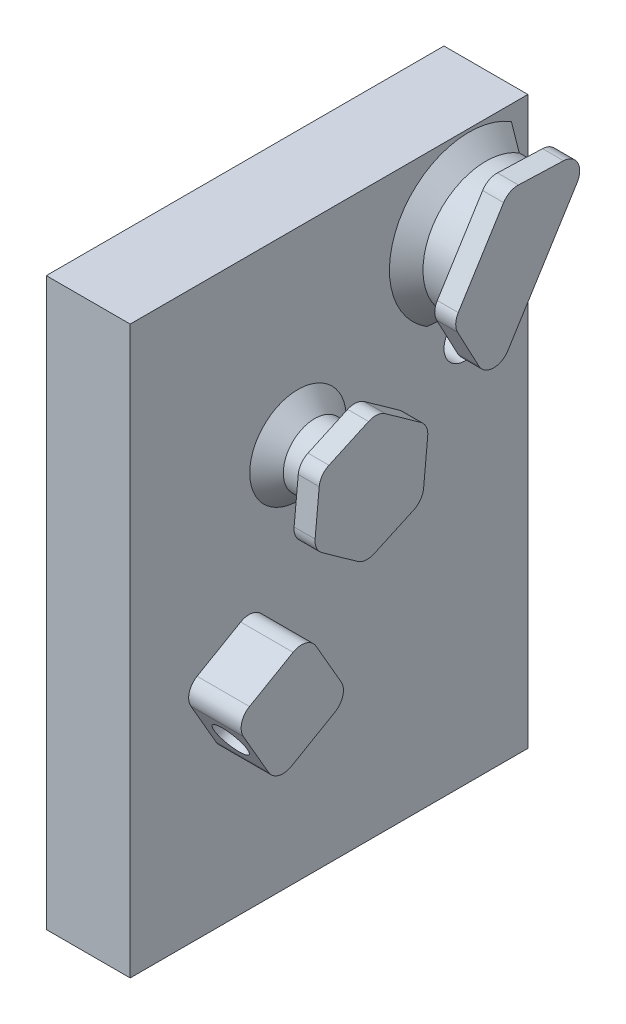
SolidWorks part; units mm, degrees
ref_plane "Front Plane" through (0, 0, 0) normal (0, 0, 1) x (1, 0, 0)
ref_plane "Top Plane" through (0, 0, 0) normal (0, 1, 0) x (1, 0, 0)
ref_plane "Right Plane" through (0, 0, 0) normal (1, 0, 0) x (0, 0, -1)
sketch "Sketch1" plane through (0, 0, 0) normal (1, 0, 0) x (0, 0, -1)
  line L0 (25.527, 46.2915) -> (60.198, 46.2915) construction
  line L1 (0, 0) -> (60.198, 0)
  line L2 (0, 0) -> (0, 85.725)
  line L3 (0, 85.725) -> (60.198, 85.725)
  line L4 (60.198, 0) -> (60.198, 85.725)
  line L5 (16.002, 51.054) -> (25.527, 51.054) construction
  line L6 (16.002, 51.054) -> (16.002, 41.529) construction
  line L7 (16.002, 41.529) -> (25.527, 41.529) construction
  line L8 (25.527, 51.054) -> (25.527, 41.529) construction
  line L9 (50.673, 46.2915) -> (50.673, 58.7375) construction
  line L11 (48.3561, 35.7396) -> (42.0218, 61.0906) construction
  circle A3 centre (50.673, 58.7375) radius 3.175
  point P16 (43.688, 135.89)
  point P17 (29.972, 160.528)
  point P18 (103.632, 160.528)
  dimension "D17" = 6.35
  dimension "D1" = 85.725
  dimension "D2" = 60.198
  dimension "D3" = 9.525
  dimension "D4" = 34.671
  dimension "D5" = 41.529
  dimension "D15" = 12.446
  dimension "D16" = 9.525
  dimension "D18" = 58.7375
extrude "Boss-Extrude1" add sketch "Sketch1" against normal blind 12.7
sketch "Sketch3" plane through (0, 0, 0) normal (1, 0, 0) x (0, 0, -1)
  line L0 (60.198, 85.725) -> (0, 85.725) construction
  line L1 (0, 85.725) -> (0, 0) construction
  line L2 (60.198, 0) -> (60.198, 85.725) construction
  line L3 (0, 0) -> (60.198, 0) construction
  line L4 (16.002, 51.054) -> (25.527, 51.054) construction
  line L5 (16.002, 51.054) -> (16.002, 41.529) construction
  line L6 (16.002, 41.529) -> (25.527, 41.529) construction
  line L7 (25.527, 51.054) -> (25.527, 41.529) construction
  line L8 (18.923, 39.5735) -> (25.273, 28.575)
  line L9 (18.923, 39.5735) -> (7.9245, 33.2235)
  line L10 (25.273, 28.575) -> (14.2745, 22.225)
  line L11 (7.9245, 33.2235) -> (14.2745, 22.225)
  line L12 (18.923, 39.5735) -> (18.923, 29.3688) construction
  line L15 (56.355, 81.2486) -> (46.2599, 65.0934)
  circle A1 centre (25.4, 57.15) radius 4.7625
  arc A4 (56.355, 81.2486) -> (46.2599, 65.0934) centre (51.3075, 73.171) ccw
  point P18 (22.098, 34.0743)
  dimension "D2" = 9.525
  dimension "D3" = 8.8905
  dimension "D4" = 19.05
  dimension "D5" = 12.554
  dimension "D6" = 28.575
  dimension "D7" = 25.4
  dimension "D10" = 9.525
  dimension "D11" = 41.529
  dimension "D12" = 34.671
  dimension "D13" = 12.7
  dimension "D14" = 38.1
  dimension "D15" = 22.225
  dimension "D16" = 30
extrude "Boss-Extrude2" add sketch "Sketch3" along normal blind 7.9375
sketch "Sketch10" plane through (7.9375, 0, 0) normal (1, 0, 0) x (0, 0, -1)
  line L2 (48.9823, 57.4672) -> (64.4028, 82.1447)
  line L3 (48.9823, 57.4672) -> (64.4028, 82.1447)
  line L4 (26.3059, 66.6318) -> (17.6415, 62.6755)
  line L5 (17.6415, 62.6755) -> (16.7355, 53.1936)
  line L6 (16.7355, 53.1936) -> (24.4941, 47.6682)
  line L7 (24.4941, 47.6682) -> (33.1585, 51.6245)
  line L8 (33.1585, 51.6245) -> (34.0645, 61.1064)
  line L9 (34.0645, 61.1064) -> (26.3059, 66.6318)
  circle A0 centre (25.4, 57.15) radius 7.9375 construction
  arc A4 (64.4028, 82.1447) -> (48.9823, 57.4672) centre (51.3075, 73.171) ccw
  arc A5 (62.1564, 84.7604) -> (48.9823, 57.4672) centre (51.3075, 73.171) ccw
  dimension "D1" = 15.875
  dimension "D3" = 9.525
  dimension "D2" = 6.35
extrude "Boss-Extrude3" add sketch "Sketch10" along normal blind 3.175 contours L4 L5 L6 L7 L8 L9
sketch "Sketch14" plane through (7.9375, 0, 0) normal (1, 0, 0) x (0, 0, -1)
  line L0 (51.3075, 73.171) -> (58.882, 85.2924)
  line L2 (51.3075, 73.171) -> (43.733, 61.0495)
  line L4 (46.1897, 85.7358) -> (37.7708, 72.263)
  line L5 (37.7708, 72.263) -> (43.733, 61.0495)
  line L9 (58.882, 85.2924) -> (46.1897, 85.7358)
  line L12 (46.2599, 65.0934) -> (56.355, 81.2486) construction
  arc A0 (43.733, 61.0495) -> (58.882, 85.2924) centre (51.3075, 73.171) cw construction
  point P2 (0, 0)
  point P3 (0, 0)
  point P6 (0, 0)
  point P9 (0, 0)
  point P12 (51.3075, 73.171)
  point P13 (87.2744, 154.6447)
  point P14 (91.8646, 155.4272)
  point P15 (96.8868, 157.1485)
  point P16 (118.3258, 169.6675)
  point P17 (106.5532, 170.7107)
  point P18 (103.4279, 169.4067)
  point P19 (98.7769, 155.5315)
  point P20 (118.6498, 170.1891)
  point P21 (113.5196, 170.0848)
  point P22 (0, 0)
  point P26 (118.0018, 169.1459)
  point P28 (116.1117, 176.5008)
  dimension "D1" = 60
  dimension "D2" = 120
  dimension "D3" = 12.7
  dimension "D4" = 120
extrude "Boss-Extrude4" add sketch "Sketch14" along normal blind 3.175
fillet "Fillet1" radius 2.54 14 edges at (9.525, 47.6682, -24.4941) (9.525, 51.6245, -33.1585) (9.525, 61.1064, -34.0645) (9.525, 66.6318, -26.3059) (9.525, 53.1936, -16.7355) (9.525, 62.6755, -17.6415) (3.9688, 22.225, -14.2745) (3.9688, 33.2235, -7.9245) (3.9688, 28.575, -25.273) (3.9688, 39.5735, -18.923) (9.525, 85.2924, -58.882) (9.525, 85.7358, -46.1897) (9.525, 72.263, -37.7708) (9.525, 61.0495, -43.733)
chamfer "Chamfer1" distance 2.54 angle 45 2 edges at (0, 57.15, -20.6375) (0, 78.2185, -43.2299)
sketch "Sketch15" plane through (0, 18.0873, -31.3281) normal (0, 0.5, -0.866) x (-1, 0, 0)
  line L0 (-7.9375, 18.4602) -> (-4.1149, 18.4602) construction
  line L1 (-7.9375, 14.6502) -> (-7.9375, 22.2702) construction
  circle A0 centre (-4.1149, 18.4602) radius 2.54
  dimension "D1" = 5.08
extrude "Cut-Extrude1" cut sketch "Sketch15" against normal up to vertex (12.7 mm away)
